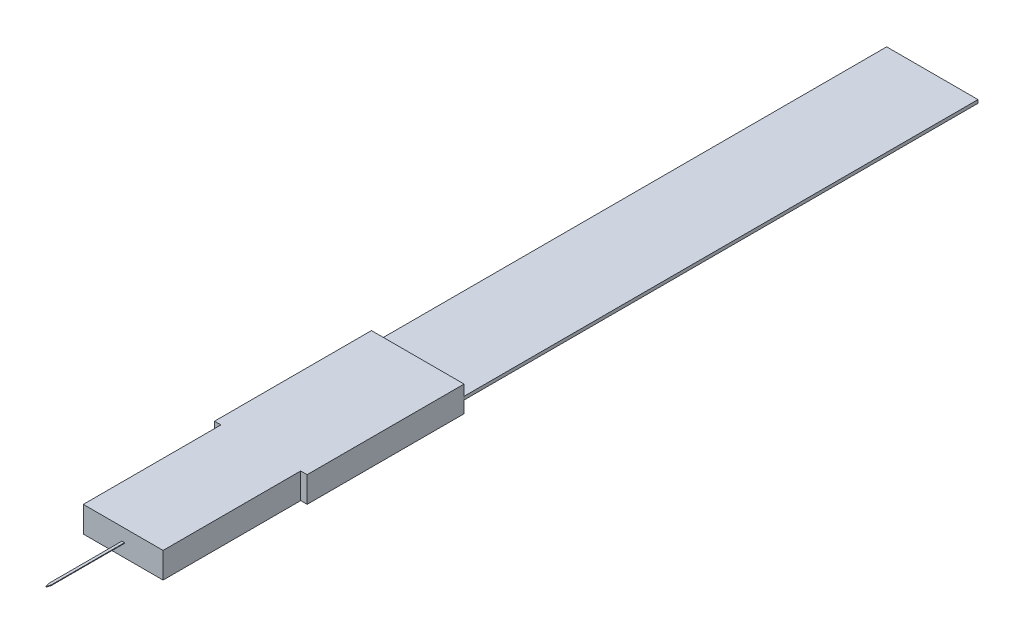
SolidWorks part; units mm, degrees
ref_plane "Front Plane" through (0, 0, 0) normal (0, 0, 1) x (1, 0, 0)
ref_plane "Top Plane" through (0, 0, 0) normal (0, 1, 0) x (1, 0, 0)
ref_plane "Right Plane" through (0, 0, 0) normal (1, 0, 0) x (0, 0, -1)
sketch "Sketch1" plane through (0, 0, 0) normal (0, 1, 0) x (1, 0, 0)
  line L0 (-3.1, -6.1) -> (3.1, -6.1)
  line L1 (-3.6, -6.1) -> (3.6, -6.1)
  line L2 (-3.6, -6.1) -> (-3.6, 6.1)
  line L3 (-3.6, 6.1) -> (3.6, 6.1)
  line L4 (3.6, -6.1) -> (3.6, 6.1)
  line L5 (0, 6.1) -> (0, -6.1) construction
  line L6 (-3.6, 0) -> (3.6, 0) construction
  line L8 (-3.1, -6.1) -> (3.1, -6.1)
  line L9 (-3.1, -6.1) -> (-3.1, -16.8)
  line L10 (-3.1, -16.8) -> (3.1, -16.8)
  line L11 (3.1, -6.1) -> (3.1, -16.8)
  point P0 (0, 0)
  point P7 (0, -6.1)
  dimension "D1" = 7.2
  dimension "D2" = 12.2
  dimension "D3" = 10.7
extrude "Boss-Extrude1" add sketch "Sketch1" along normal blind 2 contours L1 L4 L3 L2 L0 | L11 L0 L9 L10
sketch "Sketch2" plane through (0, 0, -6.1) normal (0, 0, -1) x (-1, 0, 0)
  line L0 (0, 0) -> (0, 2) construction
  line L1 (3.6, 0) -> (-3.6, 0) construction
  line L2 (3.6, 2) -> (-3.6, 2) construction
  line L4 (-3.55, 0.8732) -> (3.55, 0.8732)
  line L5 (-3.55, 0.8732) -> (-3.55, 1.1268)
  line L6 (-3.55, 1.1268) -> (3.55, 1.1268)
  line L7 (3.55, 0.8732) -> (3.55, 1.1268)
  line L8 (0, 1.1268) -> (0, 0.8732) construction
  line L9 (-3.55, 1) -> (3.55, 1) construction
  point P6 (0, 1)
  dimension "D1" = 7.1
extrude "Boss-Extrude2" add sketch "Sketch2" along normal blind 40
sketch "Sketch3" plane through (0, 0, 16.8) normal (0, 0, 1) x (1, 0, 0)
  line L0 (0, 0) -> (0, 2) construction
  line L1 (-3.1, 2) -> (3.1, 2) construction
  line L3 (-0.1, 0.975) -> (0.1, 0.975)
  line L4 (-0.1, 0.975) -> (-0.1, 1.025)
  line L5 (-0.1, 1.025) -> (0.1, 1.025)
  line L6 (0.1, 0.975) -> (0.1, 1.025)
  line L7 (0, 1.025) -> (0, 0.975) construction
  line L8 (-0.1, 1) -> (0.1, 1) construction
  point P5 (0, 1)
  dimension "D1" = 0.05
  dimension "D2" = 0.2
extrude "Boss-Extrude3" add sketch "Sketch3" along normal blind 6
sketch "Sketch4" plane through (0, 0.975, 0) normal (0, -1, 0) x (1, 0, 0)
  line L0 (0, 22.8) -> (0, 22.5) construction
  line L1 (-0.1, 22.8) -> (0.1, 22.8) construction
  line L2 (-0.1, 22.5) -> (0.1, 22.5) construction
  line L3 (-0.1, 22.8) -> (-0.1, 16.8) construction
  line L4 (0.1, 22.8) -> (0.1, 16.8) construction
  line L5 (-0.1, 22.5) -> (0, 22.8)
  line L6 (0, 22.8) -> (0.1, 22.5)
  line L7 (-0.1, 22.5) -> (-0.1, 22.8)
  line L8 (-0.1, 22.8) -> (0.1, 22.8)
  line L9 (0.1, 22.8) -> (0.1, 22.5)
  line M3 (0.1, 16.8) -> (0.1, 22.8)
  line M4 (0.1, 22.8) -> (-0.1, 22.8)
  line M5 (-0.1, 22.8) -> (-0.1, 16.8)
  dimension "D1" = 0.3
extrude "Cut-Extrude1" cut sketch "Sketch4" against normal up to surface (0.05 mm away) contours L6 M4 M3 | L5 M5 M4 up to face at (0, 1.025, 19.8)
